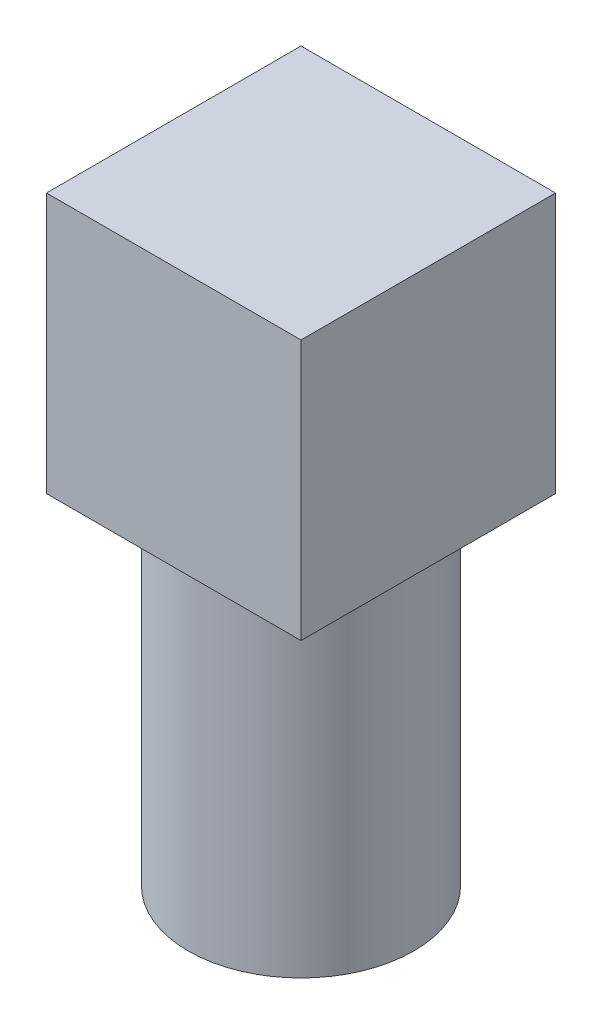
SolidWorks part; units mm, degrees
ref_plane "Front Plane" through (0, 0, 0) normal (0, 0, 1) x (1, 0, 0)
ref_plane "Top Plane" through (0, 0, 0) normal (0, 1, 0) x (1, 0, 0)
ref_plane "Right Plane" through (0, 0, 0) normal (1, 0, 0) x (0, 0, -1)
sketch "Sketch2" plane through (0, 0, 0) normal (0, 1, 0) x (1, 0, 0)
  line L1 (-22, -22) -> (22, -22)
  line L2 (-22, -22) -> (-22, 22)
  line L3 (-22, 22) -> (22, 22)
  line L4 (22, -22) -> (22, 22)
  line L5 (-22, -22) -> (22, 22) construction
  line L6 (-22, 22) -> (22, -22) construction
  point P0 (0, 0)
  dimension "D1" = 44
extrude "Boss-Extrude1" add sketch "Sketch2" along normal blind 45
sketch "Sketch3" plane through (0, 0, 0) normal (0, -1, 0) x (1, 0, 0)
  circle A0 centre (0, 0) radius 19.5
  dimension "D1" = 39
extrude "Boss-Extrude2" add sketch "Sketch3" along normal blind 58.72
